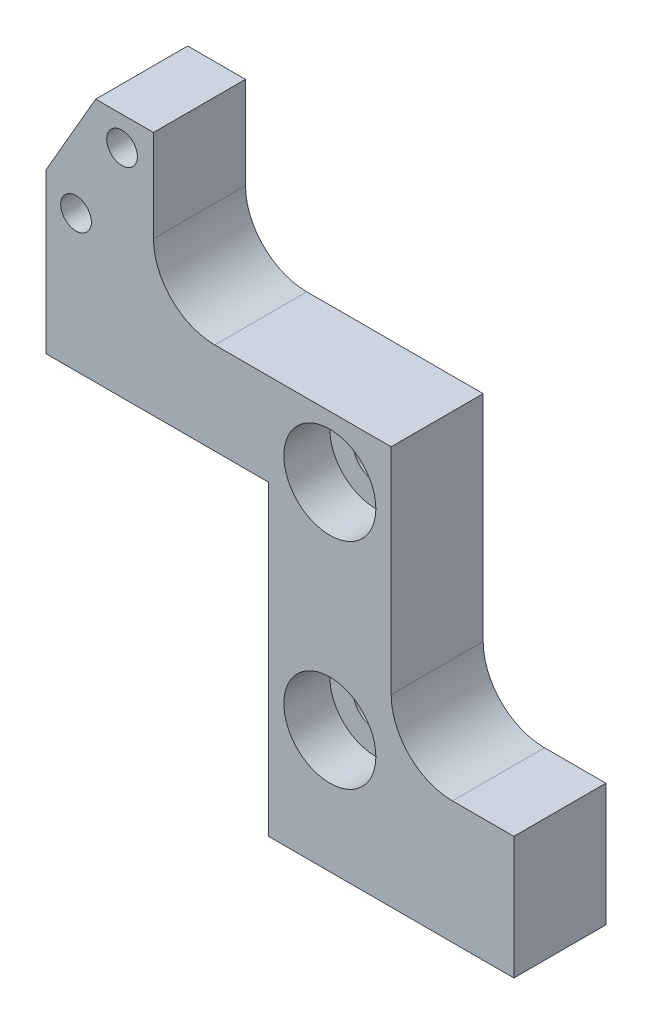
SolidWorks part; units mm, degrees
ref_plane "Front Plane" through (0, 0, 0) normal (0, 0, 1) x (1, 0, 0)
ref_plane "Top Plane" through (0, 0, 0) normal (0, 1, 0) x (1, 0, 0)
ref_plane "Right Plane" through (0, 0, 0) normal (1, 0, 0) x (0, 0, -1)
sketch "Sketch1" plane through (0, 0, 0) normal (0, 0, 1) x (1, 0, 0)
  line L0 (-27.2668, 36) -> (-30.5, 30.4)
  line L1 (0, 0) -> (-16, 0)
  line L2 (0, 0) -> (0, 8)
  line L3 (0, 8) -> (-8, 8)
  line L4 (-16, 0) -> (-16, 8)
  line L6 (-16, 8) -> (-16, 20)
  line L7 (-16, 26) -> (-8, 26)
  line L8 (-8, 8) -> (-8, 26)
  line L9 (-16, 26) -> (-23.5, 26)
  line L11 (-16, 20) -> (-30.5, 20)
  line L12 (-30.5, 26) -> (-30.5, 20)
  line L14 (-30.5, 26) -> (-30.5, 30.4)
  line L15 (-27.2668, 36) -> (-23.5, 36)
  line L16 (-23.5, 26) -> (-23.5, 36)
  circle A0 centre (-28.55, 28.91) radius 1
  circle A1 centre (-25.55, 34.1062) radius 1
  dimension "D11" = 1.95
  dimension "D15" = 2
  dimension "D16" = 2
  dimension "D1" = 16
  dimension "D2" = 8
  dimension "D3" = 18
  dimension "D4" = 8
  dimension "D5" = 20
  dimension "D6" = 14.5
  dimension "D7" = 7
  dimension "D8" = 10
  dimension "D9" = 30
  dimension "D10" = 5.6
  dimension "D12" = 7.09
  dimension "D14" = 6
extrude "Boss-Extrude1" add sketch "Sketch1" along normal blind 6
fillet "Fillet1" radius 4 1 edges at (-23.5, 26, 3)
fillet "Fillet2" radius 4 1 edges at (-8, 8, 3)
sketch "Sketch2" plane through (0, 0, 6) normal (0, 0, 1) x (1, 0, 0)
  line L0 (0, 0) -> (0, 8) construction
  line L1 (0, 8) -> (-4, 8) construction
  line L2 (-16, 0) -> (0, 0) construction
  circle A0 centre (-12, 22) radius 3
  circle A1 centre (-12, 8) radius 3
  dimension "D1" = 6
  dimension "D2" = 6
  dimension "D3" = 12
  dimension "D4" = 14
  dimension "D5" = 12
  dimension "D6" = 8
extrude "Cut-Extrude1" cut sketch "Sketch2" against normal blind 3
sketch "Sketch3" plane through (0, 0, 3) normal (0, 0, 1) x (1, 0, 0)
  circle A0 centre (-12, 22) radius 1.5
  circle A1 centre (-12, 8) radius 1.5
  dimension "D1" = 3
  dimension "D2" = 3
extrude "Cut-Extrude2" cut sketch "Sketch3" against normal through all
hole_wizard "M3x0.5 Tapped Hole1" positions "Sketch5" profile "Sketch4" tap size "M3x0.5" standard "ANSI Metric"
sketch "Sketch5" plane through (0, 0, 0) normal (0, -1, 0) x (-1, 0, 0)
  line L0 (0, -6) -> (0, 0) construction
  line L2 (16, 0) -> (0, 0) construction
  point P0 (13, -3)
  point P2 (3, -3)
  dimension "D1" = 3
  dimension "D2" = 13
  dimension "D3" = 3
sketch "Sketch4" plane through (-13, 0, 3) normal (1, 0, 0) x (0, 0, -1)
  line L0 (0, 0) -> (0, 4.7511)
  line L1 (0, 4.7511) -> (1.25, 4)
  line L2 (1.25, 4) -> (1.25, 0.275)
  line L3 (1.25, 0.275) -> (1.525, 0)
  line L5 (1.525, 0) -> (0, 0)
  line L6 (-1.25, 0.275) -> (-1.525, 0) construction
  line L10 (0, 4.7511) -> (-1.25, 4) construction
  line L11 (0, -6.35) -> (0, 107.95) construction
  dimension "Tap Drill Dia." = 2.5
  dimension "Tap Drill Depth" = 4
  dimension "Near C'Sink Dia." = 3.05
  dimension "Near C'Sink Angle" = 90
  dimension "Drill Angle" = 118
cosmetic thread "Hole Thread1" parameters "D1"=4, "D2"=3
cosmetic thread "Hole Thread2" parameters "D1"=4, "D2"=3
hole_wizard "Ø2.0 (2) Diameter Hole1" positions "Sketch7" profile "Sketch6" hole size "Ø2.0" standard "ANSI Metric"
sketch "Sketch7" plane through (0, 0, 0) normal (0, -1, 0) x (-1, 0, 0)
  line L0 (16, 0) -> (0, 0) construction
  line L1 (0, -6) -> (0, 0) construction
  point P0 (8, -3)
  dimension "D1" = 3
  dimension "D2" = 8
sketch "Sketch6" plane through (-8, 0, 3) normal (1, 0, 0) x (0, 0, -1)
  line L0 (0, 0) -> (0, 3.6009)
  line L1 (0, 3.6009) -> (1, 3)
  line L2 (1, 3) -> (1, 0)
  line L5 (1, 0) -> (0, 0)
  line L10 (0, 3.6009) -> (-1, 3) construction
  line L11 (0, -6.35) -> (0, 107.95) construction
  dimension "Hole Dia." = 2
  dimension "Hole Depth" = 3
  dimension "Drill Angle" = 118
